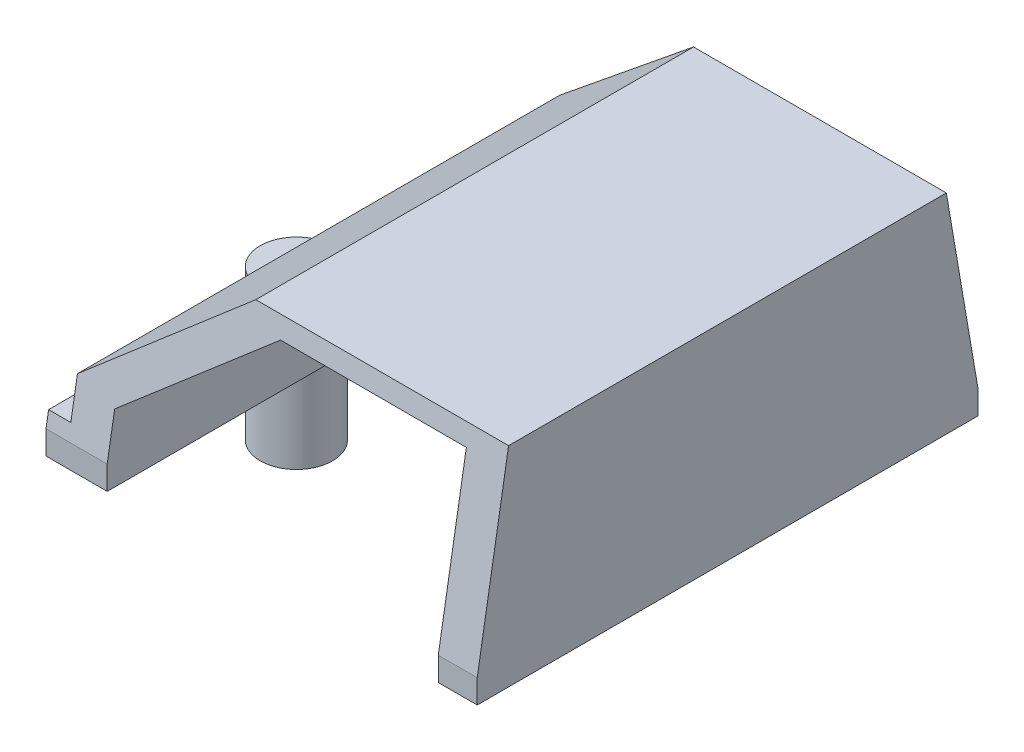
SolidWorks part; units mm, degrees
material "Very Low Density PE (SS)"
ref_plane "Front Plane" through (0, 0, 0) normal (0, 0, 1) x (1, 0, 0)
ref_plane "Top Plane" through (0, 0, 0) normal (0, 1, 0) x (1, 0, 0)
ref_plane "Right Plane" through (0, 0, 0) normal (1, 0, 0) x (0, 0, -1)
sketch "Sketch1" plane through (0, 0, -0.183) normal (0, 1, 0) x (1, 0, 0)
  line L0 (-13.7891, -8.5735) -> (-13.7891, -31.4335)
  line L1 (-13.7891, -31.4335) -> (6.5309, -31.4335)
  line L2 (-13.7891, -8.5735) -> (6.5309, -8.5735)
  line L3 (6.5309, -8.5735) -> (6.5309, -31.4335)
  circle A0 centre (-13.7891, -20.0035) radius 1.651
sketch "Sketch2" plane through (0, 0, 0) normal (0, 1, 0) x (1, 0, 0)
  circle A0 centre (-13.7891, -19.8204) radius 1.651
extrude "Boss-Extrude1" add sketch "Sketch1" along normal blind 9.5387 contours A0 | L3 L1 L0 L2
extrude "Boss-Extrude2" add sketch "Sketch2" against normal blind 5.08 separate body
sketch "Sketch3" plane through (0, 0, 31.2504) normal (0, 0, 1) x (1, 0, 0)
  line L0 (6.1542, 0) -> (4.3484, 0)
  line L1 (-13.7891, 9.5387) -> (6.5309, 9.5387) construction
  line L2 (4.3484, 9.5387) -> (4.3484, 7.112)
  line L3 (-13.7891, 0) -> (6.5309, 0) construction
  line L4 (-13.7891, 0) -> (-10.9951, 0)
  line L5 (-12.1381, 0) -> (-15.4401, 0) construction
  line L6 (-13.7891, 0) -> (-13.7891, 1.778)
  line L7 (-13.7891, 9.5387) -> (-13.7891, 0) construction
  line L8 (-13.7891, 1.778) -> (-12.7731, 1.778)
  line L9 (4.3484, 0) -> (4.3484, 7.112)
  line L10 (-12.7731, 1.778) -> (-10.9951, 1.778) construction
  line L11 (-6.962, 7.112) -> (4.3484, 7.112)
  line L12 (-12.7731, 3.556) -> (-7.2266, 9.5387)
  line L13 (-12.7731, 1.778) -> (-12.7731, 3.556)
  line L14 (-10.9951, 3.175) -> (-6.962, 7.112)
  line L15 (-10.9951, 0) -> (-10.9951, 3.175)
  line L16 (-10.9951, 3.175) -> (-10.9951, 3.2441)
  line L17 (-9.6432, 6.9794) -> (-8.4013, 5.7071) construction
  line L18 (4.3484, 9.5387) -> (-7.2266, 9.5387)
  line L19 (-6.962, 7.112) -> (-8.74, 7.112) construction
  line L20 (4.3484, 3.8881) -> (6.5309, 3.8881) construction
  line L21 (6.5309, 9.5387) -> (6.5309, 0) construction
  line L22 (4.3484, 0) -> (-13.7891, 0)
  line L23 (4.3484, -5.08) -> (-13.7891, -5.08)
  line L24 (4.3484, 0) -> (6.1542, 0)
  line L25 (5.6541, 9.5387) -> (4.3484, 9.5387)
  dimension "D1" = 5.08
sketch "Sketch8" plane through (0, 0, 31.2504) normal (0, 0, 1) x (1, 0, 0)
  line L0 (-10.9951, 0) -> (4.3484, 0)
  line L1 (4.3484, 0) -> (4.3484, 7.112)
  line L2 (4.3484, 7.112) -> (-6.962, 7.112)
  line L3 (-6.962, 7.112) -> (-10.9951, 3.175)
  line L4 (-10.9951, 3.175) -> (-10.9951, 0)
sketch "Sketch9" plane through (0, 0, 31.2504) normal (0, 0, 1) x (1, 0, 0)
  line L0 (-12.7731, 1.778) -> (-15.4401, 1.778)
  line L1 (-15.4401, 9.5387) -> (-15.4401, 0) construction
  line L2 (-15.4401, 1.778) -> (-15.4401, 9.5387)
  line L3 (-13.7891, 9.5387) -> (-15.4401, 9.5387) construction
  line L4 (-15.4401, 9.5387) -> (-7.2266, 9.5387)
  line L5 (-7.2266, 9.5387) -> (-12.7731, 3.556)
  line L6 (-12.7731, 3.556) -> (-12.7731, 1.778)
extrude "Cut-Extrude8" cut sketch "Sketch9" against normal through all
sketch "Sketch10" plane through (0, 9.5387, -0.183) normal (0, 1, 0) x (1, 0, 0)
  line L0 (-7.2266, -20.0035) -> (-7.2266, -11.4638)
  line L1 (-7.2266, -8.5735) -> (-7.2266, -31.4335) construction
  line L2 (-7.2266, -20.0035) -> (-7.2266, -29.3664)
  line L3 (6.5309, -29.3664) -> (6.5309, -30.0013)
  line L4 (6.5309, -8.5735) -> (6.5309, -31.4335) construction
  line L5 (-7.2266, -29.3664) -> (6.5309, -30.0013)
  line L6 (6.5309, -11.4638) -> (6.5309, -10.8289)
  line L7 (-7.2266, -11.4638) -> (6.5309, -10.8289)
  line L8 (-7.2266, -11.4638) -> (-13.7891, -8.5735)
  line L9 (-13.7891, -8.5735) -> (-7.2266, -10.3821)
  line L10 (-7.2266, -10.3821) -> (6.5309, -10.8289)
  line L11 (-13.7891, -31.4335) -> (-7.2266, -30.423)
  line L12 (-7.2266, -30.423) -> (6.5309, -31.4335)
  line L13 (4.3484, -31.4335) -> (6.1542, -31.4335) construction
  line L14 (6.5309, -31.4335) -> (-13.7891, -31.4335)
  line L15 (6.5309, -8.5735) -> (-7.2266, -10.3821)
  line L16 (-13.7891, -8.5735) -> (6.5309, -8.5735)
sketch "Sketch23" plane through (6.5309, 0, 0) normal (1, 0, 0) x (0, 0, -1)
  line L0 (-31.2504, 0) -> (-31.2504, 1.0816)
  line L1 (-31.2504, 3.175) -> (-31.2504, 0) construction
  line L2 (-31.2504, 1.0816) -> (-8.3904, 1.0816)
  line L3 (-8.3904, 9.5387) -> (-8.3904, 0) construction
  line L4 (-8.3904, 1.0816) -> (-9.8356, 9.5387)
  line L5 (-11.2808, 9.5387) -> (-8.3904, 9.5387) construction
  line L6 (-9.8356, 9.5387) -> (-8.3904, 9.5387)
  line L7 (-8.3904, 9.5387) -> (-8.3904, 1.0816)
  line L8 (-31.2504, 1.0816) -> (-29.8183, 9.5387)
  line L9 (-29.1833, 9.5387) -> (-29.8183, 9.5387) construction
  line L10 (-8.3904, 9.5387) -> (-31.2504, 9.5387) construction
  line L11 (-29.8183, 9.5387) -> (-31.2504, 9.5387)
  line L12 (-31.2504, 9.5387) -> (-31.2504, 1.0816)
  line M2 (-8.3904, 0) -> (-8.3904, 9.5387)
  line M3 (-8.3904, 9.5387) -> (-31.2504, 9.5387)
  line M4 (-31.2504, 9.5387) -> (-31.2504, 0)
extrude "Cut-Extrude17" cut sketch "Sketch23" against normal through all contours L8 M4 M3 | L4 M2 M3
sketch "Sketch24" plane through (0, 0, 31.2504) normal (0, 0, 1) x (1, 0, 0)
  line L0 (6.5309, 0) -> (5.8959, 0)
  line L1 (-10.9951, 0) -> (4.3484, 0) construction
  line L2 (5.8959, 0) -> (5.8959, 9.5387)
  line L3 (-7.2266, 9.5387) -> (6.5309, 9.5387) construction
  line L4 (5.8959, 9.5387) -> (6.5309, 9.5387)
  line L5 (6.5309, 9.5387) -> (6.5309, 0)
sketch "Sketch26" plane through (0, 0, 31.2504) normal (0, 0, 1) x (1, 0, 0)
  line L0 (-12.7731, 3.556) -> (-6.6444, 9.5387)
  line L1 (-7.2266, 9.5387) -> (6.5309, 9.5387) construction
  line L2 (-6.6444, 9.5387) -> (-7.2266, 9.5387)
  line L3 (-7.2266, 9.5387) -> (-12.7731, 3.556)
extrude "Cut-Extrude19" cut sketch "Sketch26" against normal through all
sketch "Sketch28" plane through (0, 0, 31.2504) normal (0, 0, 1) x (1, 0, 0)
  line L0 (-6.6444, 9.5387) -> (-5.6444, 9.5387)
  line L1 (-6.6444, 9.5387) -> (6.5309, 9.5387) construction
  line L2 (-5.6444, 9.5387) -> (-12.7731, 3.556)
  line L3 (-12.7731, 3.556) -> (-6.6444, 9.5387)
sketch "Sketch29" plane through (0, 0, 31.2504) normal (0, 0, 1) x (1, 0, 0)
  line L0 (-12.7731, 2.667) -> (-10.9951, 2.667)
  line L1 (-12.7731, 1.778) -> (-12.7731, 3.556) construction
  line L2 (-10.9951, 3.175) -> (-10.9951, 0) construction
  line L18 (-12.7731, 2.667) -> (-5.6888, 9.5825)
  line L19 (-5.6888, 9.5825) -> (-3.7718, 9.5387)
  line L20 (-6.6444, 9.5387) -> (6.5309, 9.5387) construction
  line L23 (-6.2381, 5.334) -> (-9.2171, 2.4259)
  line L24 (2.5704, 5.334) -> (-6.2381, 5.334)
  line L25 (2.5704, 1.778) -> (2.5704, 5.334)
  line L26 (-9.2171, 1.778) -> (2.5704, 1.778)
  line L27 (-9.2171, 2.4259) -> (-9.2171, 1.778)
  line L28 (-6.2381, 5.334) -> (-9.2171, 2.4259)
  line L29 (2.5704, 5.334) -> (-6.2381, 5.334)
  line L30 (2.5704, 1.778) -> (2.5704, 5.334)
  line L32 (-9.2171, 2.4259) -> (-9.2171, 1.778)
  dimension "D1" = 1.778
extrude "Cut-Extrude21" cut sketch "Sketch24" against normal through all
extrude "Cut-Extrude22" cut sketch "Sketch28" against normal through all contours L2 L3 L0
sketch "Sketch31" plane through (0, 0, 31.2504) normal (0, 0, 1) x (1, 0, 0)
  line L0 (5.8959, 0) -> (4.1179, 0)
  line L1 (-13.7891, 0) -> (5.8959, 0) construction
  line L2 (-10.9951, 0) -> (4.1179, 0)
  line L4 (-10.9951, 1.778) -> (-10.9951, 0)
  line L6 (-10.9951, 0) -> (-10.9951, 3.091)
  line L8 (-5.4309, 7.7607) -> (4.1179, 7.7607)
  line L9 (4.1179, 7.7607) -> (4.1179, 0)
  line L14 (-8.245, 5.399) -> (-10.9951, 3.091)
  line L15 (-10.9951, 3.091) -> (-5.4309, 7.7607)
  line M5 (-13.7891, 0) -> (5.8959, 0)
  line M7 (5.8959, 1.0816) -> (-13.7891, 1.0816)
extrude "Cut-Extrude23" cut sketch "Sketch31" against normal through all contours L15 L14 L6 L4 L9 L8 M7 | L9 L4 M7 M5
sketch "Sketch33" plane through (0, 0, 31.2504) normal (0, 0, 1) x (1, 0, 0)
  line L0 (-5.4309, 7.7607) -> (-4.3639, 8.6562)
  line L1 (4.1179, 7.7607) -> (-5.4357, 7.7607)
  line L2 (4.1179, 7.7607) -> (4.1179, 8.6562)
  line L3 (4.1179, 8.6562) -> (-4.3639, 8.6562)
extrude "Cut-Extrude24" cut sketch "Sketch33" against normal through all contours L2 L3 L0 L1
